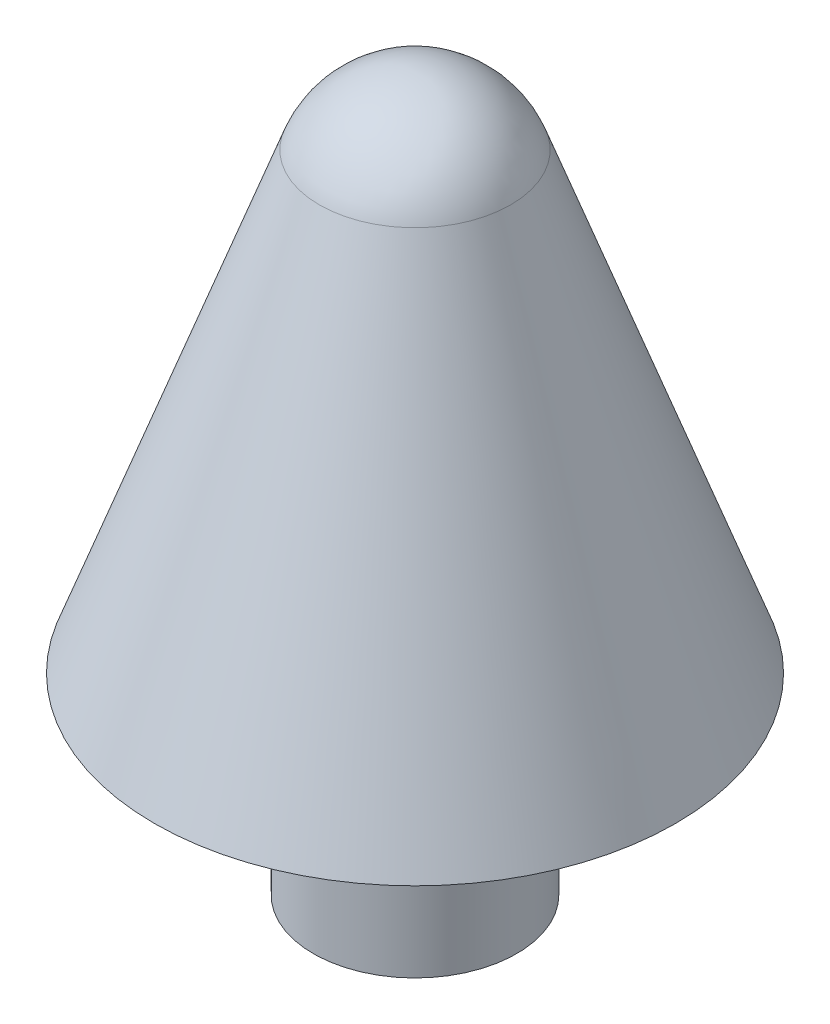
SolidWorks part; units mm, degrees
material "ABS"
ref_plane "Front Plane" through (0, 0, 0) normal (0, 0, 1) x (1, 0, 0)
ref_plane "Top Plane" through (0, 0, 0) normal (0, 1, 0) x (1, 0, 0)
ref_plane "Right Plane" through (0, 0, 0) normal (1, 0, 0) x (0, 0, -1)
sketch "Sketch1" plane through (0, 0, 0) normal (0, 0, 1) x (1, 0, 0)
  line L0 (0, 0) -> (3.175, 0)
  line L1 (3.175, 0) -> (3.175, 5.9944)
  line L2 (3.175, 5.9944) -> (8.1306, 5.9944)
  line L3 (8.1306, 5.9944) -> (2.9835, 20.1359)
  line L4 (0, 22.225) -> (0, 0)
  arc A0 (2.9835, 20.1359) -> (0, 22.225) centre (0, 19.05) ccw
  dimension "D6" = 3.175
  dimension "D1" = 5.9944
  dimension "D2" = 70
  dimension "D3" = 20
  dimension "D4" = 19.05
  dimension "D5" = 3.175
revolve "Revolve1" add sketch "Sketch1" angle 360 about L4
